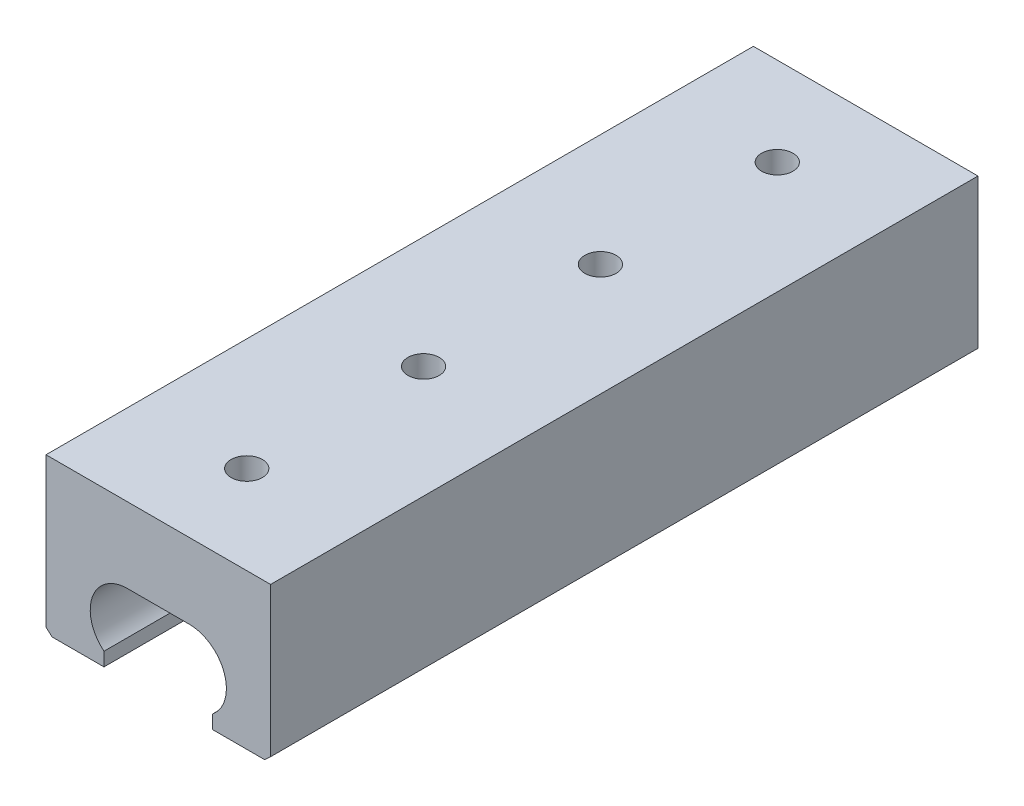
SolidWorks part; units mm, degrees
ref_plane "Front" through (0, 0, 0) normal (0, 0, 1) x (1, 0, 0)
ref_plane "Top" through (0, 0, 0) normal (0, 1, 0) x (1, 0, 0)
ref_plane "Right" through (0, 0, 0) normal (1, 0, 0) x (0, 0, -1)
sketch "Sketch1" plane through (0, 0, 0) normal (0, 0, 1) x (1, 0, 0)
  line L0 (-51.8484, -29.0299) -> (-51.8484, -32.937)
  line L1 (-68.5064, 11.513) -> (-3.9904, 11.513)
  line L2 (-20.6484, -29.0299) -> (-20.6484, -32.937)
  line L3 (-51.8484, -32.937) -> (-66.7991, -32.937)
  line L5 (-36.2484, 11.513) -> (-36.2484, -41.6818) construction
  line L6 (-45.1384, -10.0684) -> (-27.3584, -10.0684)
  line L7 (-3.9904, 11.513) -> (-3.9904, -31.3555)
  line L8 (-68.5064, 11.513) -> (-68.5064, -31.3555)
  line L9 (-20.6484, -32.937) -> (-5.6976, -32.937)
  line L11 (-68.5064, -31.3555) -> (-66.7991, -32.937)
  line L12 (-3.9904, -31.3555) -> (-5.6976, -32.937)
  arc A1 (-27.3584, -10.0684) -> (-20.6484, -29.0299) centre (-27.3584, -20.7364) cw
  arc A2 (-45.1384, -10.0684) -> (-51.8484, -29.0299) centre (-45.1384, -20.7364) ccw
  point P12 (-36.2484, -10.0684)
  dimension "D6" = 10.668
  dimension "D1" = 44.45
  dimension "D3" = 64.516
  dimension "D5" = 17.78
extrude "Base-Extrude" add sketch "Sketch1" along normal blind 203.2
sketch "Sketch2" plane through (0, 11.513, 0) normal (0, 1, 0) x (-1, 0, 0)
  circle A0 centre (36.2484, 177.8) radius 5.5 construction
  circle A1 centre (36.2484, 177.8) radius 5.5 construction
hole_wizard "Tap Drill for M10x1.0 Tap2" positions "Sketch4" profile "Sketch3" hole size "M10x1.0" standard "Ansi Metric" end condition through all
sketch "Sketch4" plane through (0, 11.513, 0) normal (0, 1, 0) x (-1, 0, 0)
  point P0 (36.2484, 177.8)
sketch "Sketch3" plane through (-36.2484, 11.513, 177.8) normal (1, 0, 0) x (0, 0, 1)
  line L0 (0, 0) -> (0, 44.45)
  line L1 (0, 44.45) -> (4.5, 44.45)
  line L2 (4.5, 44.45) -> (4.5, 0)
  line L5 (4.5, 0) -> (0, 0)
  line L11 (0, -6.35) -> (0, 107.95) construction
  dimension "Thru Hole Dia." = 9
  dimension "Thru Hole Depth" = 44.45
pattern_linear "LPattern1" count 4 spacing 50.8 along (0, 0, -1) of "Tap Drill for M10x1.0 Tap2"
sketch "Sketch5" [suppressed] plane through (0, 11.513, 0) normal (0, 1, 0) x (-1, 0, 0)
  circle A0 centre (36.2484, 177.8) radius 5.5 construction
  circle A1 centre (36.2484, 177.8) radius 5.5 construction
hole_wizard "Tap Drill for M10x1.0 Tap1" [suppressed] positions "Sketch7" profile "Sketch6" hole size "M10x1.0" standard "Ansi Metric"
sketch "Sketch7" plane through (0, 11.513, 0) normal (0, 1, 0) x (-1, 0, 0)
  point P0 (36.2484, 177.8)
sketch "Sketch6" plane through (-36.2484, 11.513, 177.8) normal (1, 0, 0) x (0, 0, 1)
  line L0 (0, 0) -> (0, 44.45)
  line L1 (0, 44.45) -> (4.5, 44.45)
  line L2 (4.5, 44.45) -> (4.5, 0)
  line L5 (4.5, 0) -> (0, 0)
  line L11 (0, -6.35) -> (0, 107.95) construction
  dimension "Thru Hole Dia." = 9
  dimension "Thru Hole Depth" = 44.45
pattern_linear "LPattern2" [suppressed] count 4 spacing 50.8
